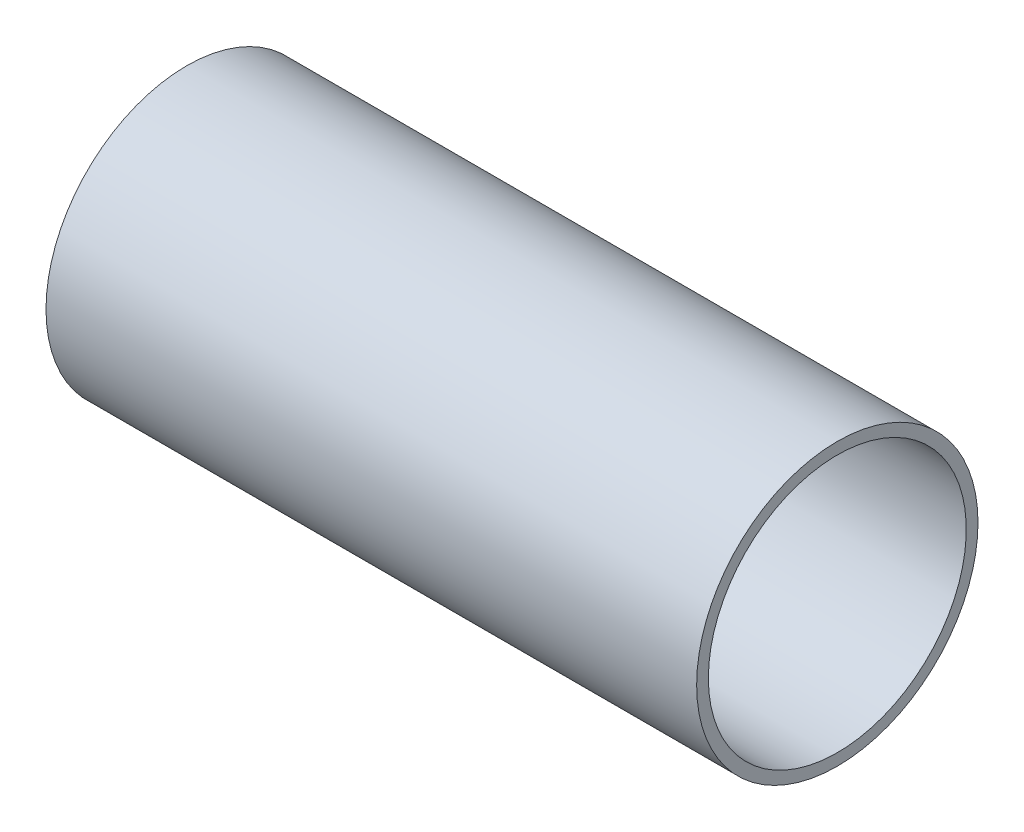
SolidWorks part; units mm, degrees
material "6061 Alloy"
ref_plane "Front Plane" through (0, 0, 0) normal (0, 0, 1) x (1, 0, 0)
ref_plane "Top Plane" through (0, 0, 0) normal (0, 1, 0) x (1, 0, 0)
ref_plane "Right Plane" through (0, 0, 0) normal (1, 0, 0) x (0, 0, -1)
sketch "Sketch1" plane through (0, 0, 0) normal (1, 0, 0) x (0, 0, -1)
  circle A0 centre (0, 0) radius 38.1
  dimension "D1" = 76.2
extrude "Boss-Extrude1" add sketch "Sketch1" along normal mid plane 176.2125 contours A0
shell "Shell2" thickness 3.175
ref_plane "Plane1" through (-0.0064, 0, 0) normal (1, 0, 0) x (0, 0, -1)
